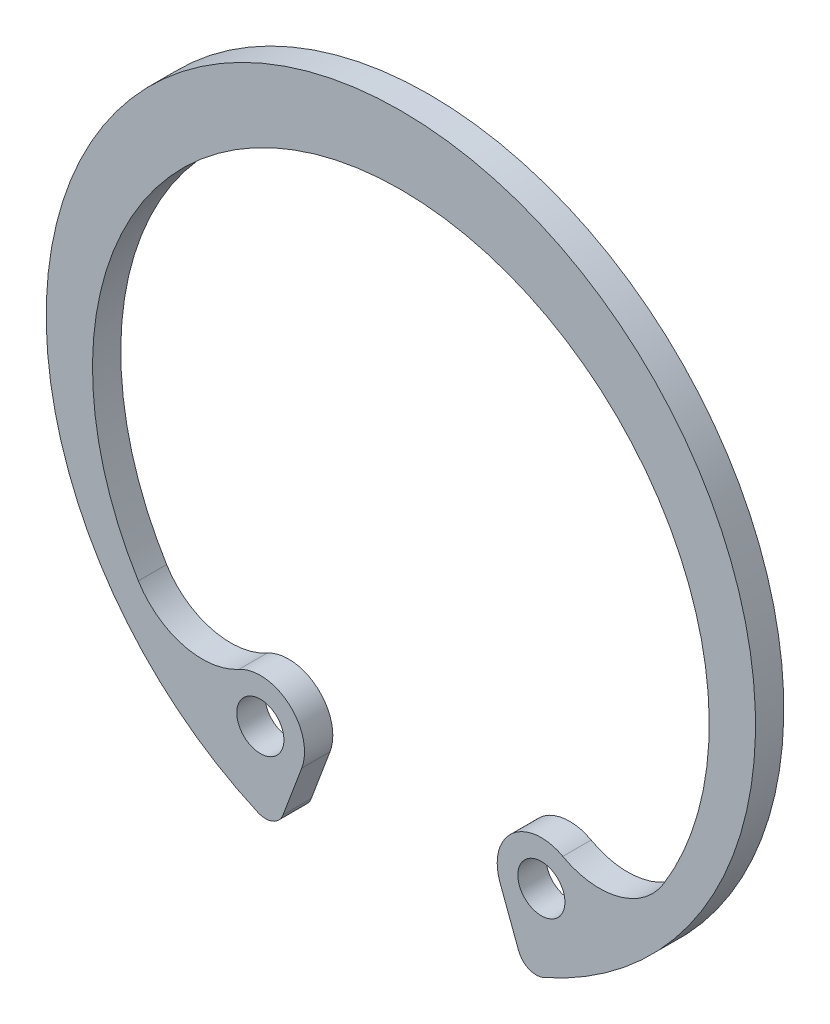
SolidWorks part; units mm, degrees
ref_plane "Front Plane" through (0, 0, 0) normal (0, 0, 1) x (1, 0, 0)
ref_plane "Top Plane" through (0, 0, 0) normal (0, 1, 0) x (1, 0, 0)
ref_plane "Right Plane" through (0, 0, 0) normal (1, 0, 0) x (0, 0, -1)
sketch "Sketch1" plane through (0, 0, 0) normal (0, 0, 1) x (1, 0, 0)
  line L0 (0, 15.05) -> (0, 12.15) construction
  line L1 (-12.3282, -8.6323) -> (-11.1405, -7.8006) construction
  line L2 (0, 0) -> (0, -15.05) construction
  line L3 (-3.6, -9.597) -> (-5.2859, -14.0912) construction
  line L4 (-3.6, -9.597) -> (-5.6, -9.597) construction
  circle A0 centre (0, 0) radius 14.7 construction
  circle A1 centre (0, 0) radius 15.05 construction
  circle A2 centre (0, 0) radius 14 construction
  dimension "Ring OD" = 30.1
  dimension "For ID" = 28
  dimension "Maximum Section" = 2.9
  dimension "D1" = 125
  dimension "Minimum Section" = 1.45
  dimension "Gap Width" = 7.2
  dimension "Lug Height" = 4.8
  dimension "Hole Diameter" = 2
sketch "Sketch2" plane through (0, 0, 0) normal (1, 0, 0) x (0, 0, -1)
  line L0 (-0.65, 15.05) -> (0.65, 15.05) construction
  line L1 (-0.6, -15.05) -> (0.6, -15.05) construction
  point P3 (0, 15.05)
  point P7 (0, -15.05)
  point P8 (-0.6, -15.05)
  point P10 (0.6, -15.05)
  point P11 (-0.65, 15.05)
  point P12 (0.65, 15.05)
  dimension "For Groove Width" = 1.3
  dimension "Ring Thickness" = 1.2
sketch "Sketch3" plane through (0, 0, 0) normal (0, 0, 1) x (1, 0, 0)
  line L0 (-5.2859, -14.0912) -> (-3.6438, -9.7139) construction
  line L1 (-3.6438, -9.7139) -> (-6.3207, -8.2019) construction
  line L2 (0, 0) -> (-5.0408, -8.9249) construction
  line L3 (-11.1405, -7.8006) -> (11.1405, -7.8006) construction
  line L4 (0, 0) -> (0, -15.05) construction
  line L5 (-6.3207, -8.2019) -> (0, 0) construction
  line L6 (-5.0408, -8.9249) -> (-5.9629, -10.5575) construction
  line L7 (-5.9629, -10.5575) -> (-6.885, -12.1901) construction
  line L8 (0, 15.05) -> (0, 12.15) construction
  line L11 (-4.2073, -11.216) -> (-5.2859, -14.0912)
  line L12 (0, 0) -> (0, -7.8006) construction
  line L13 (4.2073, -11.216) -> (5.2859, -14.0912)
  line L14 (-3.6, -9.597) -> (-5.2859, -14.0912) construction
  line L15 (-5.0408, -8.9249) -> (-7.4013, -13.1043) construction
  arc A0 (-5.2859, -14.0912) -> (5.2859, -14.0912) centre (0, 0) cw
  circle A1 centre (0, 0) radius 15.05 construction
  arc A2 (-11.1405, -7.8006) -> (11.1405, -7.8006) centre (0, -0.9357) cw
  circle A4 centre (-5.9629, -10.5575) radius 1
  circle A5 centre (0, 0) radius 13.6 construction
  circle A7 centre (5.9629, -10.5575) radius 1
  circle A8 centre (0, 0) radius 14 construction
  arc A9 (-6.8725, -8.9179) -> (-4.2073, -11.216) centre (-5.9629, -10.5575) cw
  arc A10 (-11.1405, -7.8006) -> (-6.8725, -8.9179) centre (-8.4217, -6.1253) ccw
  arc A11 (6.8725, -8.9179) -> (4.2073, -11.216) centre (5.9629, -10.5575) ccw
  arc A12 (11.1405, -7.8006) -> (6.8725, -8.9179) centre (8.4217, -6.1253) cw
  point P3 (0, -7.8006)
  dimension "D1" = 2
  dimension "D2" = 4.8
extrude "Boss-Extrude1" add sketch "Sketch3" against normal up to vertex (0.6 mm away) and the other way up to vertex (0.6 mm away) up to point (0, -15.05, -0.6) other way up to point (0, -15.05, 0.6)
fillet "Fillet1" radius 0.7937 2 edges at (5.2859, -14.0912, 0) (-5.2859, -14.0912, 0)
equation "\"D1@Sketch3\"=\"Hole Diameter@Sketch1\""
equation "\"Minimum Section@Sketch1\"=\"Maximum Section@Sketch1\"*.5"
equation "\"Gap Width@Sketch1\"=\"Lug Height@Sketch1\"*1.5"
equation "\"D2@Sketch3\"=\"Lug Height@Sketch1\""
